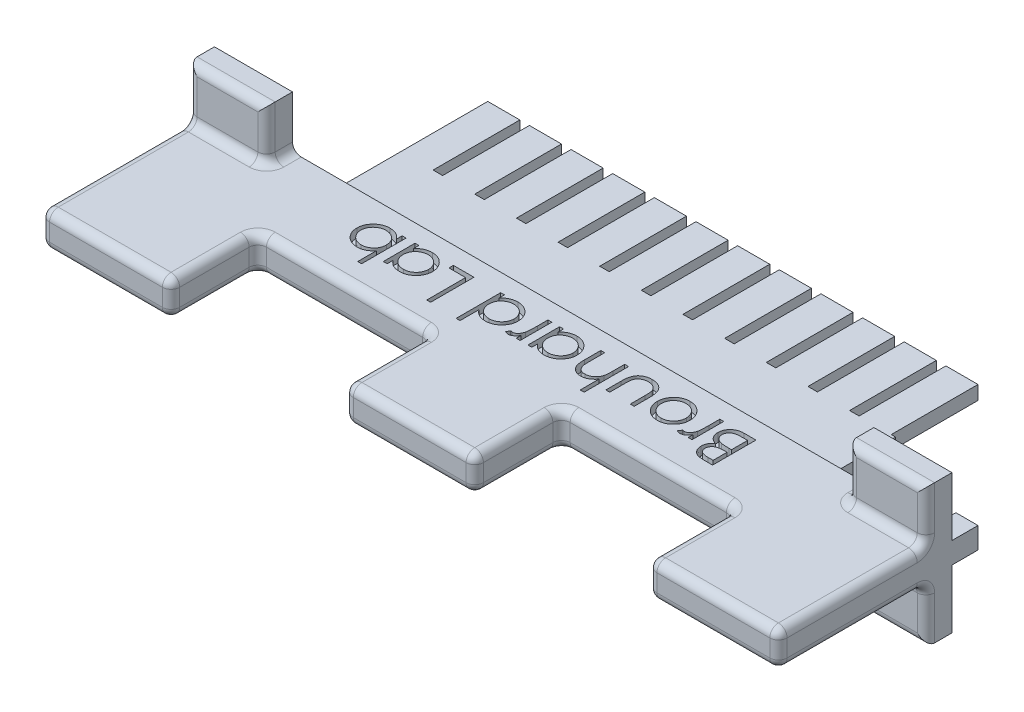
SolidWorks part; units mm, degrees
ref_plane "Front Plane" through (0, 0, 0) normal (0, 0, 1) x (1, 0, 0)
ref_plane "Top Plane" through (0, 0, 0) normal (0, 1, 0) x (1, 0, 0)
ref_plane "Right Plane" through (0, 0, 0) normal (1, 0, 0) x (0, 0, -1)
sketch "Sketch1" plane through (0, 0, 0) normal (0, 0, 1) x (1, 0, 0)
  line L1 (-42.5, 2) -> (42.5, 2)
  line L2 (-42.5, 2) -> (-42.5, -2)
  line L3 (-42.5, -2) -> (42.5, -2)
  line L4 (42.5, 2) -> (42.5, -2)
  line L5 (-42.5, 2) -> (42.5, -2) construction
  line L6 (-42.5, -2) -> (42.5, 2) construction
  point P0 (0, 0)
  dimension "D1" = 85
  dimension "D2" = 4
extrude "Boss-Extrude1" add sketch "Sketch1" along normal blind 10
sketch "Sketch2" plane through (0, 0, 10) normal (0, 0, 1) x (1, 0, 0)
  line L0 (-42.5, -2) -> (42.5, -2) construction
  line L1 (-42.5, 2) -> (-27.5, 2)
  line L2 (-42.5, 2) -> (-42.5, -2)
  line L3 (-42.5, -2) -> (-27.5, -2)
  line L4 (-27.5, 2) -> (-27.5, -2)
  line L6 (42.5, 2) -> (27.5, 2)
  line L7 (42.5, 2) -> (42.5, -2)
  line L8 (42.5, -2) -> (27.5, -2)
  line L9 (27.5, 2) -> (27.5, -2)
  line L10 (-7.5, 2) -> (7.5, 2)
  line L11 (-7.5, 2) -> (-7.5, -2)
  line L12 (-7.5, -2) -> (7.5, -2)
  line L13 (7.5, 2) -> (7.5, -2)
  line L14 (-7.5, 2) -> (7.5, -2) construction
  line L15 (-7.5, -2) -> (7.5, 2) construction
  point P12 (0, 0)
  dimension "D1" = 15
extrude "Boss-Extrude2" add sketch "Sketch2" along normal blind 10
sketch "Sketch3" plane through (0, 0, 0) normal (0, 0, -1) x (-1, 0, 0)
  line L9 (42.5, -1.225) -> (39.95, -1.225)
  line L10 (42.5, -1.225) -> (42.5, 1.225)
  line L11 (42.5, 1.225) -> (39.95, 1.225)
  line L12 (39.95, -1.225) -> (39.95, 1.225)
  line L13 (42.5, -1.225) -> (39.95, 1.225) construction
  line L14 (42.5, 1.225) -> (39.95, -1.225) construction
  line L15 (42.5, 2) -> (42.5, -2) construction
  line L16 (0, 0) -> (0, 13.9589)
  line L17 (-42.5, 1.225) -> (-39.95, -1.225) construction
  line L18 (-42.5, -1.225) -> (-39.95, 1.225) construction
  line L19 (-39.95, -1.225) -> (-39.95, 1.225)
  line L20 (-42.5, 1.225) -> (-39.95, 1.225)
  line L21 (-42.5, -1.225) -> (-42.5, 1.225)
  line L22 (-42.5, -1.225) -> (-39.95, -1.225)
  point P3 (42.5, 0)
  point P10 (41.225, 0)
  point P16 (-41.225, 0)
  line M3 (-42.5, 2) -> (-42.5, -2)
  dimension "D1" = 2.45
  dimension "D2" = 2.55
extrude "Boss-Extrude3" add sketch "Sketch3" along normal blind 3 contours L22 L19 L20 M3 | L12 L11 L10 L9
sketch "Sketch4" plane through (0, 0, 0) normal (0, 0, -1) x (-1, 0, 0)
  line L1 (28.5, -0.8) -> (-28.5, -0.8)
  line L2 (28.5, -0.8) -> (28.5, 0.8)
  line L3 (28.5, 0.8) -> (-28.5, 0.8)
  line L4 (-28.5, -0.8) -> (-28.5, 0.8)
  line L5 (28.5, -0.8) -> (-28.5, 0.8) construction
  line L6 (28.5, 0.8) -> (-28.5, -0.8) construction
  point P0 (0, 0)
  dimension "D1" = 1.6
  dimension "D2" = 57
extrude "Boss-Extrude4" add sketch "Sketch4" along normal blind 7.5
sketch "Sketch6" plane through (0, 0, 0) normal (0, 0, -1) x (-1, 0, 0)
  line L1 (42.5, -2) -> (33.5, -2)
  line L2 (42.5, -2) -> (42.5, -8)
  line L3 (42.5, -8) -> (33.5, -8)
  line L4 (33.5, -2) -> (33.5, -8)
  line L5 (42.5, 2) -> (33.5, 2)
  line L6 (42.5, 2) -> (42.5, 8)
  line L7 (42.5, 8) -> (33.5, 8)
  line L8 (33.5, 2) -> (33.5, 8)
  line L9 (-42.5, -2) -> (-33.5, -2)
  line L10 (-42.5, -2) -> (-42.5, -8)
  line L11 (-42.5, -8) -> (-33.5, -8)
  line L12 (-33.5, -2) -> (-33.5, -8)
  line L13 (-42.5, 2) -> (-33.5, 2)
  line L14 (-42.5, 2) -> (-42.5, 8)
  line L15 (-42.5, 8) -> (-33.5, 8)
  line L16 (-33.5, 2) -> (-33.5, 8)
  dimension "D1" = 6
  dimension "D2" = 9
extrude "Boss-Extrude6" add sketch "Sketch6" against normal blind 3
fillet "Fillet1" radius 1 52 edges at (-42.5, -2, 11.5) (-33.5, -2, 1.5) (-38, -2, 3) (-33.5, -5, 3) (-38, -8, 3) (-42.5, -5, 3) (-27.5, 0, 20) (-35, -2, 20) (-42.5, 0, 20) (-35, 2, 20) (33.5, -2, 1.5) (42.5, -2, 11.5) (42.5, 2, 11.5) (33.5, 2, 1.5) (-33.5, 2, 1.5) (-42.5, 2, 11.5) (38, -8, 3) (33.5, -5, 3) (38, -2, 3) (42.5, -5, 3) (35, -2, 20) (27.5, 0, 20) (35, 2, 20) (42.5, 0, 20) (38, 2, 3) (33.5, 5, 3) (38, 8, 3) (42.5, 5, 3) (0, -2, 20) (-7.5, 0, 20) (0, 2, 20) (7.5, 0, 20) (-38, 8, 3) (-33.5, 5, 3) (-38, 2, 3) (-42.5, 5, 3) (27.5, 2, 15) (27.5, -2, 15) (27.5, 0, 10) (17.5, -2, 10) (17.5, 2, 10) (7.5, -2, 15) (7.5, 2, 15) (7.5, 0, 10) (-7.5, 2, 15) (-7.5, -2, 15) (-27.5, -2, 15) (-27.5, 2, 15) (-27.5, 0, 10) (-17.5, 2, 10) (-7.5, 0, 10) (-17.5, -2, 10)
ref_plane "Plane1" through (0, 0, 0) normal (0, 1, 0) x (1, 0, 0)
sketch "Sketch7" plane through (0, 2, 0) normal (0, 1, 0) x (1, 0, 0)
  line L0 (30.9142, -2.045) -> (-30.9142, -2.045)
  line L1 (32.5, 0) -> (-32.5, 0) construction
  point P2 (0, -2.045)
  point P5 (0, 0)
sketch "Sketch8" plane through (0, 2, 0) normal (0, 1, 0) x (1, 0, 0)
  text T0 "Brouhard Lab" font "Century Gothic" height 5
extrude "Cut-Extrude1" cut sketch "Sketch8" against normal blind 1
sketch "Sketch5" plane through (0, 0, -7.5) normal (0, 0, -1) x (-1, 0, 0)
  line L0 (28.5, 0.8) -> (-28.5, 0.8) construction
  line L1 (28.5, -0.8) -> (24.8, -0.8)
  line L2 (28.5, -0.8) -> (28.5, 0.8)
  line L3 (28.5, 0.8) -> (24.8, 0.8)
  line L4 (24.8, -0.8) -> (24.8, 0.8)
  line L97 (23.7, -0.8) -> (20, -0.8)
  line L98 (23.7, -0.8) -> (23.7, 0.8)
  line L99 (23.7, 0.8) -> (20, 0.8)
  line L100 (20, -0.8) -> (20, 0.8)
  line L101 (18.9, -0.8) -> (15.2, -0.8)
  line L102 (18.9, -0.8) -> (18.9, 0.8)
  line L103 (18.9, 0.8) -> (15.2, 0.8)
  line L104 (15.2, -0.8) -> (15.2, 0.8)
  line L105 (14.1, -0.8) -> (10.4, -0.8)
  line L106 (14.1, -0.8) -> (14.1, 0.8)
  line L107 (14.1, 0.8) -> (10.4, 0.8)
  line L108 (10.4, -0.8) -> (10.4, 0.8)
  line L109 (9.3, -0.8) -> (5.6, -0.8)
  line L110 (9.3, -0.8) -> (9.3, 0.8)
  line L111 (9.3, 0.8) -> (5.6, 0.8)
  line L112 (5.6, -0.8) -> (5.6, 0.8)
  line L113 (4.5, -0.8) -> (0.8, -0.8)
  line L114 (4.5, -0.8) -> (4.5, 0.8)
  line L115 (4.5, 0.8) -> (0.8, 0.8)
  line L116 (0.8, -0.8) -> (0.8, 0.8)
  line L117 (-0.3, -0.8) -> (-4, -0.8)
  line L118 (-0.3, -0.8) -> (-0.3, 0.8)
  line L119 (-0.3, 0.8) -> (-4, 0.8)
  line L120 (-4, -0.8) -> (-4, 0.8)
  line L121 (-5.1, -0.8) -> (-8.8, -0.8)
  line L122 (-5.1, -0.8) -> (-5.1, 0.8)
  line L123 (-5.1, 0.8) -> (-8.8, 0.8)
  line L124 (-8.8, -0.8) -> (-8.8, 0.8)
  line L125 (-9.9, -0.8) -> (-13.6, -0.8)
  line L126 (-9.9, -0.8) -> (-9.9, 0.8)
  line L127 (-9.9, 0.8) -> (-13.6, 0.8)
  line L128 (-13.6, -0.8) -> (-13.6, 0.8)
  line L129 (-14.7, -0.8) -> (-18.4, -0.8)
  line L130 (-14.7, -0.8) -> (-14.7, 0.8)
  line L131 (-14.7, 0.8) -> (-18.4, 0.8)
  line L132 (-18.4, -0.8) -> (-18.4, 0.8)
  line L133 (-19.5, -0.8) -> (-23.2, -0.8)
  line L134 (-19.5, -0.8) -> (-19.5, 0.8)
  line L135 (-19.5, 0.8) -> (-23.2, 0.8)
  line L136 (-23.2, -0.8) -> (-23.2, 0.8)
  line L137 (-24.3, -0.8) -> (-28, -0.8)
  line L138 (-24.3, -0.8) -> (-24.3, 0.8)
  line L139 (-24.3, 0.8) -> (-28, 0.8)
  line L140 (-28, -0.8) -> (-28, 0.8)
  dimension "D2" = 3.7
  dimension "D1" = 12
extrude "Boss-Extrude5" add sketch "Sketch5" along normal blind 10
